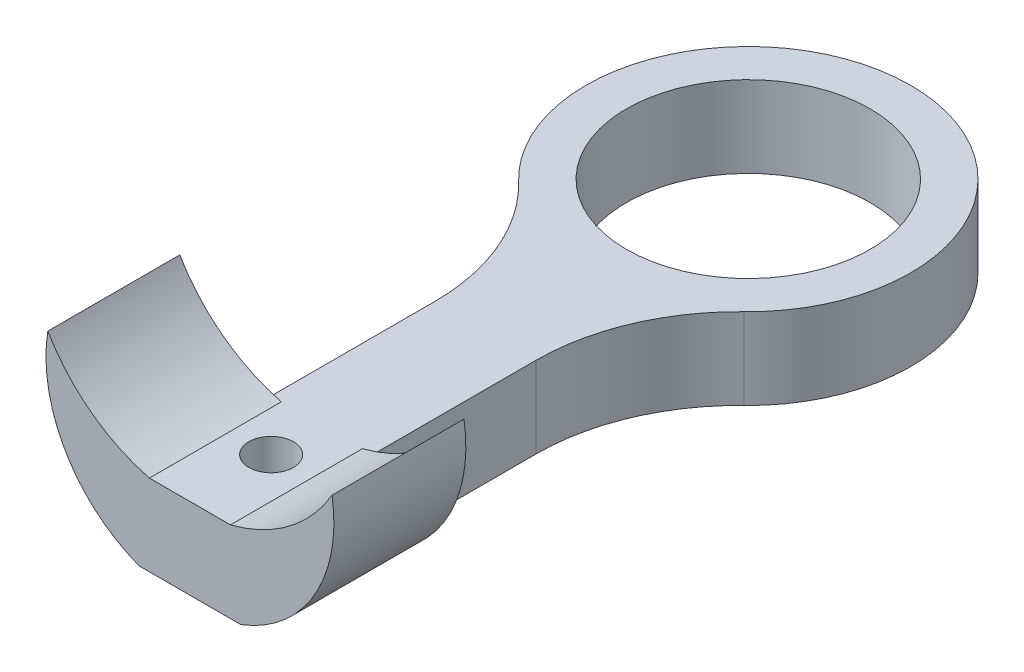
SolidWorks part; units mm, degrees
material "Nylon 101"
ref_plane "Front Plane" through (0, 0, 0) normal (0, 0, 1) x (1, 0, 0)
ref_plane "Top Plane" through (0, 0, 0) normal (0, 1, 0) x (1, 0, 0)
ref_plane "Right Plane" through (0, 0, 0) normal (1, 0, 0) x (0, 0, -1)
sketch "Sketch1" plane through (0, 0, 0) normal (0, 1, 0) x (1, 0, 0)
  line L0 (-2.5, -27.5) -> (2.5, -27.5)
  line L2 (-2.5, -12.9518) -> (-2.5, -27.5)
  line L4 (2.5, -12.9518) -> (2.5, -27.5)
  circle A0 centre (0, 0) radius 6
  arc A1 (5.5556, -5.7564) -> (-5.5556, -5.7564) centre (0, 0) ccw
  circle A2 centre (0, -23.5) radius 1.1
  arc A4 (5.5556, -5.7564) -> (2.5, -12.9518) centre (12.5, -12.9518) ccw
  arc A5 (-5.5556, -5.7564) -> (-2.5, -12.9518) centre (-12.5, -12.9518) cw
  dimension "D1" = 2
  dimension "D2" = 12
  dimension "D4" = 2.2
  dimension "D5" = 10
  dimension "D3" = 23.5
  dimension "D6" = 5
  dimension "D9" = 4
extrude "Boss-Extrude1" add sketch "Sketch1" along normal blind 4
sketch "Sketch2" plane through (0, 0, 27.5) normal (0, 0, 1) x (1, 0, 0)
  line L0 (-2.5, 0) -> (2.5, 0) construction
  line L1 (-1.9978, 4) -> (-2.5, 0)
  arc A0 (-7, 7.7669) -> (-1.9978, 4) centre (0, 11.8577) ccw construction
  arc A1 (-7, 7.7669) -> (-1.9978, 4) centre (0, 11.8577) ccw
  arc A2 (-7, 7.7669) -> (-2.5, 0) centre (0, 6.6355) ccw
  point P9 (0, 0)
extrude "Boss-Extrude2" add sketch "Sketch2" against normal up to surface (6.5 mm away)
mirror "Mirror1" about plane through (0, 0, 0) normal (1, 0, 0) of "Boss-Extrude2"
